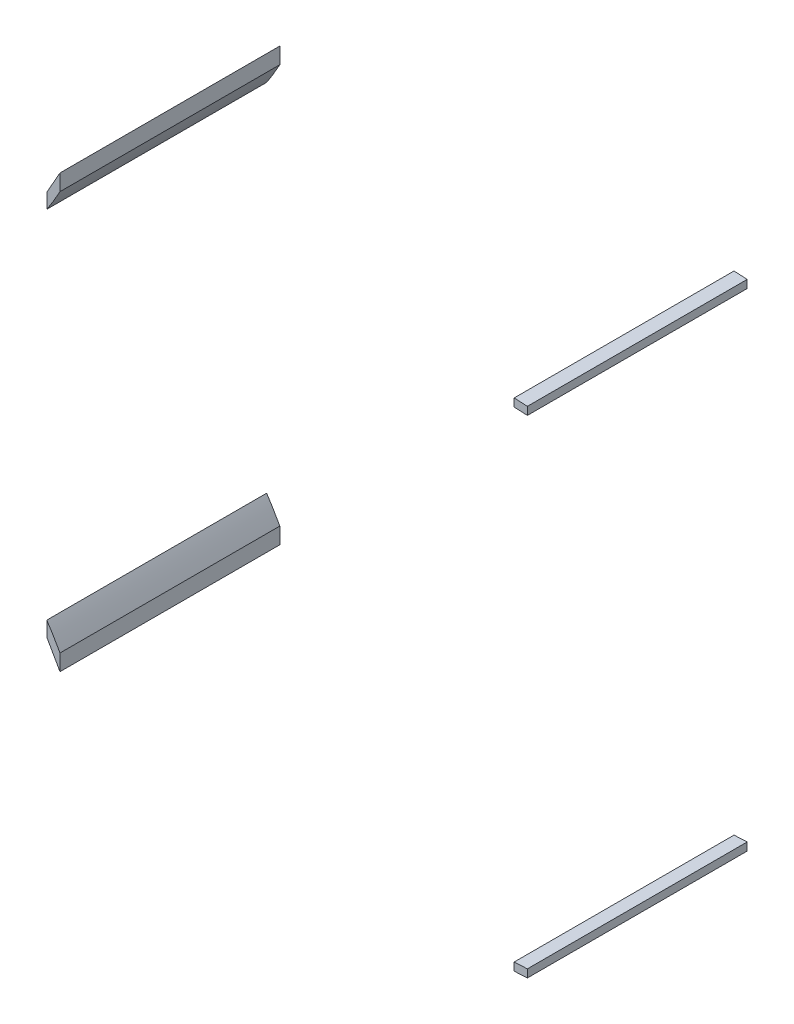
SolidWorks part; units mm, degrees
ref_plane "Front Plane" through (0, 0, 0) normal (0, 0, 1) x (1, 0, 0)
ref_plane "Top Plane" through (0, 0, 0) normal (0, 1, 0) x (1, 0, 0)
ref_plane "Right Plane" through (0, 0, 0) normal (1, 0, 0) x (0, 0, -1)
sketch "Sketch3" plane through (0, 0, 0) normal (0, 0, 1) x (1, 0, 0)
  line L0 (10.6026, 50.2098) -> (10.6026, 52.0121)
  line L1 (13.6026, 50.0581) -> (10.6026, 50.2098)
  line L2 (13.6026, 51.8604) -> (13.6026, 50.0581)
  line L3 (10.6026, 52.0121) -> (13.6026, 51.8604)
  line L4 (-92.6974, -49.8788) -> (-92.6974, -53.5657)
  line L5 (10.6026, -59.096) -> (10.6026, -60.8983)
  line L6 (-92.6974, 40.9926) -> (-92.6974, 44.6794)
  line L12 (10.6026, -60.8983) -> (13.6026, -60.7467)
  line L13 (13.6026, -60.7467) -> (13.6026, -58.9444)
  line L14 (13.6026, -58.9444) -> (10.6026, -59.096)
  line L15 (-95.6974, -44.899) -> (-95.6974, -48.2662)
  line L17 (-95.6974, 36.0127) -> (-95.6974, 39.38)
  spline S0 degree 3 poles (-95.6974, 39.38) (-94.6586, 41.1231) (-93.7007, 42.9149) (-92.6974, 44.6794) knots 0 0 0 0 0.230073 0.230073 0.230073 0.230073
  spline S1 degree 3 poles (-92.6974, 40.9926) (-93.6436, 39.301) (-94.6091, 37.6208) (-95.6974, 36.0127) knots 0.788967 0.788967 0.788967 0.788967 1 1 1 1
  spline S6 degree 3 poles (-92.6974, -49.8788) (-93.6436, -48.1873) (-94.6091, -46.507) (-95.6974, -44.899) knots 0.788967 0.788967 0.788967 0.788967 1 1 1 1
  spline S7 degree 3 poles (-95.6974, -48.2662) (-94.6586, -50.0093) (-93.7007, -51.8012) (-92.6974, -53.5657) knots 0 0 0 0 0.230073 0.230073 0.230073 0.230073
  point P4 (13.6026, -59.8455)
  dimension "D2" = 3
  dimension "D3" = 3
extrude "Boss-Extrude1" add sketch "Sketch3" along normal blind 50
